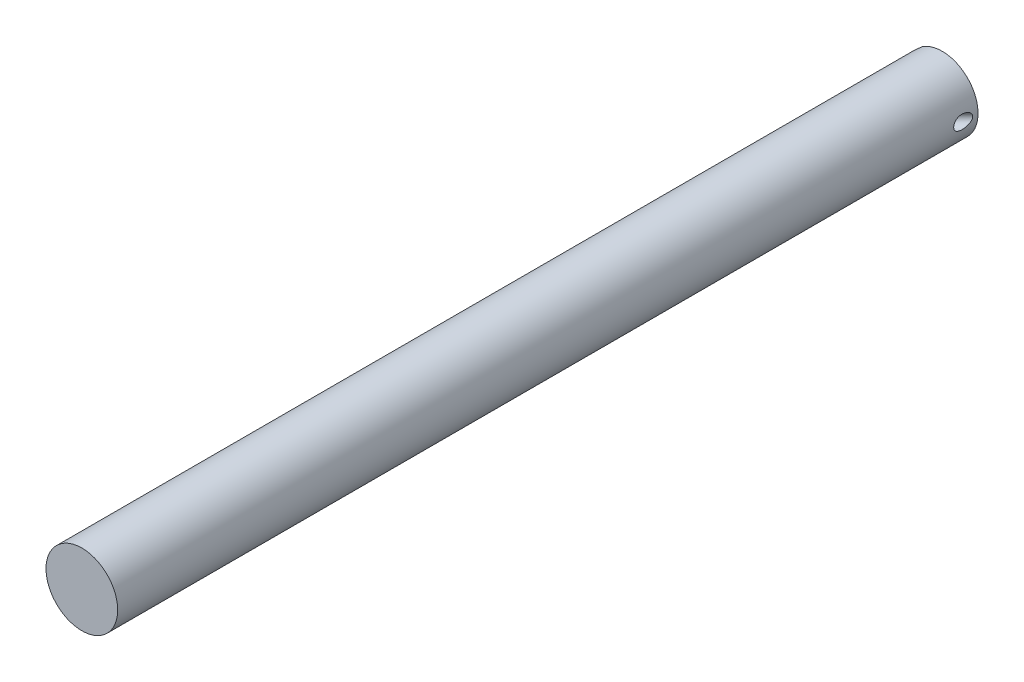
SolidWorks part; units mm, degrees
material "Plain Carbon Steel"
ref_plane "Front Plane" through (0, 0, 0) normal (0, 0, 1) x (1, 0, 0)
ref_plane "Top Plane" through (0, 0, 0) normal (0, 1, 0) x (1, 0, 0)
ref_plane "Right Plane" through (0, 0, 0) normal (1, 0, 0) x (0, 0, -1)
sketch "Sketch1" plane through (0, 0, 0) normal (0, 0, 1) x (1, 0, 0)
  circle A0 centre (0, 0) radius 12.7
  dimension "D1" = 25.4
extrude "Extrude1" add sketch "Sketch1" along normal blind 304.8
sketch "Sketch3" plane through (0, 0, 0) normal (0, 0, -1) x (-1, 0, 0)
  line L0 (0, 12.7) -> (0, -12.7) construction
  circle A0 centre (0, 0) radius 12.7 construction
ref_plane "Plane1" through (0, 0, 0) normal (-0.7071, 0, 0.7071) x (0.7071, 0, 0.7071)
sketch "Sketch4" plane through (0, 0, 0) normal (-0.7071, 0, 0.7071) x (0.7071, 0, 0.7071)
  line L0 (0, 0) -> (12.7, 0) construction
  line L1 (0, 12.7) -> (0, -12.7) construction
  circle A0 centre (12.7, 0) radius 2.3813
  dimension "D1" = 4.7625
  dimension "D2" = 12.7
extrude "Extrude2" cut sketch "Sketch4" against normal through all and the other way through all
ref_plane "Plane2" through (0, 0, 0) normal (-0.7071, 0, -0.7071) x (-0.7071, 0, 0.7071)
ref_plane "Plane3" through (-3.5921, 0, -3.5921) normal (-0.7071, 0, -0.7071) x (-0.7071, 0, 0.7071)
sketch "Sketch6" plane through (-3.5921, 0, -3.5921) normal (-0.7071, 0, -0.7071) x (-0.7071, 0, 0.7071)
  line L1 (-4.916, -18.6652) -> (15.251, -18.6652)
  line L2 (-4.916, -18.6652) -> (-4.916, 18.6652)
  line L3 (-4.916, 18.6652) -> (15.251, 18.6652)
  line L4 (15.251, -18.6652) -> (15.251, 18.6652)
  line L5 (-4.916, -18.6652) -> (15.251, 18.6652) construction
  line L6 (-4.916, 18.6652) -> (15.251, -18.6652) construction
  point P0 (5.1675, 0)
extrude "Extrude3" cut sketch "Sketch6" along normal blind 63.5
sketch "Sketch7" plane through (-3.5921, 0, -3.5921) normal (-0.7071, 0, -0.7071) x (-0.7071, 0, 0.7071)
  line L0 (5.08, 0) -> (8.382, 0) construction
  line L1 (5.08, -10.4727) -> (5.08, 10.4727) construction
  dimension "D1" = 3.302
hole_wizard "#10-24 Tapped Hole1" positions "3DSketch1" profile "Sketch9" tap size "#10-24" standard "Ansi Inch"
sketch3d "3DSketch1"
  point P0 (-9.8469, -0.2443, 2.6627)
sketch "Sketch9" plane through (-9.8469, -0.2443, 2.6627) normal (0, 1, 0) x (-0.7071, 0, 0.7071)
  line L0 (0, 0) -> (0, 15.4113)
  line L1 (0, 15.4113) -> (1.8986, 15.4113)
  line L2 (1.8986, 15.4113) -> (1.8986, 0)
  line L5 (1.8986, 0) -> (0, 0)
  line L11 (0, -6.35) -> (0, 107.95) construction
  dimension "Thru Tap Drill Dia." = 3.7973
  dimension "Thru Tap Drill Depth" = 15.4113
cosmetic thread "Hole Thread1" parameters "D2"=4.826
ref_plane "Plane4" through (-19.7566, 0, 19.7566) normal (-0.7071, 0, 0.7071) x (0.7071, 0, 0.7071)
sketch "Sketch10" plane through (-19.7566, 0, 19.7566) normal (-0.7071, 0, 0.7071) x (0.7071, 0, 0.7071)
  circle A0 centre (12.7, 0) radius 3.9688
  dimension "D1" = 7.9375
extrude "Extrude4" cut sketch "Sketch10" along normal through all
